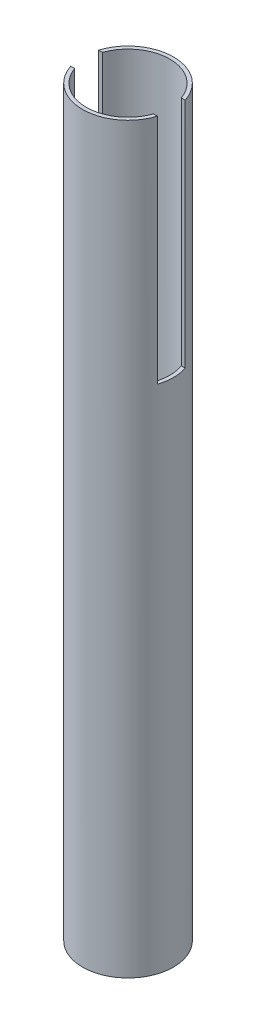
SolidWorks part; units mm, degrees
ref_plane "Front Plane" through (0, 0, 0) normal (0, 0, 1) x (1, 0, 0)
ref_plane "Top Plane" through (0, 0, 0) normal (0, 1, 0) x (1, 0, 0)
ref_plane "Right Plane" through (0, 0, 0) normal (1, 0, 0) x (0, 0, -1)
sketch "Sketch1" plane through (0, 0, 0) normal (0, 1, 0) x (1, 0, 0)
  circle A0 centre (0, 0) radius 21
  dimension "D1" = 42
extrude "Boss-Extrude1" add sketch "Sketch1" along normal blind 245
sketch "Sketch2" plane through (0, 0, 0) normal (0, 1, 0) x (1, 0, 0)
  circle A0 centre (0, 0) radius 22.5
  circle A1 centre (0, 0) radius 24.5
  dimension "D1" = 45
  dimension "D2" = 49
extrude "Boss-Extrude2" add sketch "Sketch2" along normal blind 400 separate body contours A0 | A1
sketch "Sketch3" plane through (0, 400, 0) normal (0, 1, 0) x (1, 0, 0)
  line L1 (31.5, -7.5) -> (-31.5, -7.5)
  line L2 (31.5, -7.5) -> (31.5, 7.5)
  line L3 (31.5, 7.5) -> (-31.5, 7.5)
  line L4 (-31.5, -7.5) -> (-31.5, 7.5)
  dimension "D1" = 7.5
  dimension "D2" = 15
  dimension "D3" = 63
  dimension "D4" = 31.5
extrude "Cut-Extrude1" cut sketch "Sketch3" against normal blind 125
sketch "Sketch4" plane through (0, 275, 0) normal (0, 1, 0) x (1, 0, 0)
  line L0 (-27.9688, 16.1478) -> (0, 0)
  line L1 (0, 0) -> (28.9677, -16.7245)
  line L2 (0, 0) -> (-32.9437, -19.0201)
  line L3 (0, 0) -> (27.0572, 15.6215)
  line L5 (0, 0) -> (-33.2818, 0)
  line L6 (-31.4889, 6) -> (31.9631, 6)
  line L7 (-31.4889, -6) -> (31.9631, -6)
  circle A0 centre (0, 0) radius 20.5
  circle A2 centre (0, 0) radius 26.5
  arc A3 (-21.2132, 7.5) -> (-21.2132, -7.5) centre (0, 0) ccw construction
  arc A4 (-23.3238, 7.5) -> (-23.3238, -7.5) centre (0, 0) ccw construction
  circle A5 centre (0, 0) radius 22
  circle A6 centre (0, 0) radius 25
  arc A7 (23.3238, 7.5) -> (-23.3238, 7.5) centre (0, 0) ccw construction
  arc A8 (21.2132, 7.5) -> (-21.2132, 7.5) centre (0, 0) ccw construction
  dimension "D1" = 2
  dimension "D2" = 2
  dimension "D3" = 0.5
  dimension "D4" = 0.5
  dimension "D5" = 30
  dimension "D6" = 30
  dimension "D7" = 6
  dimension "D8" = 6
